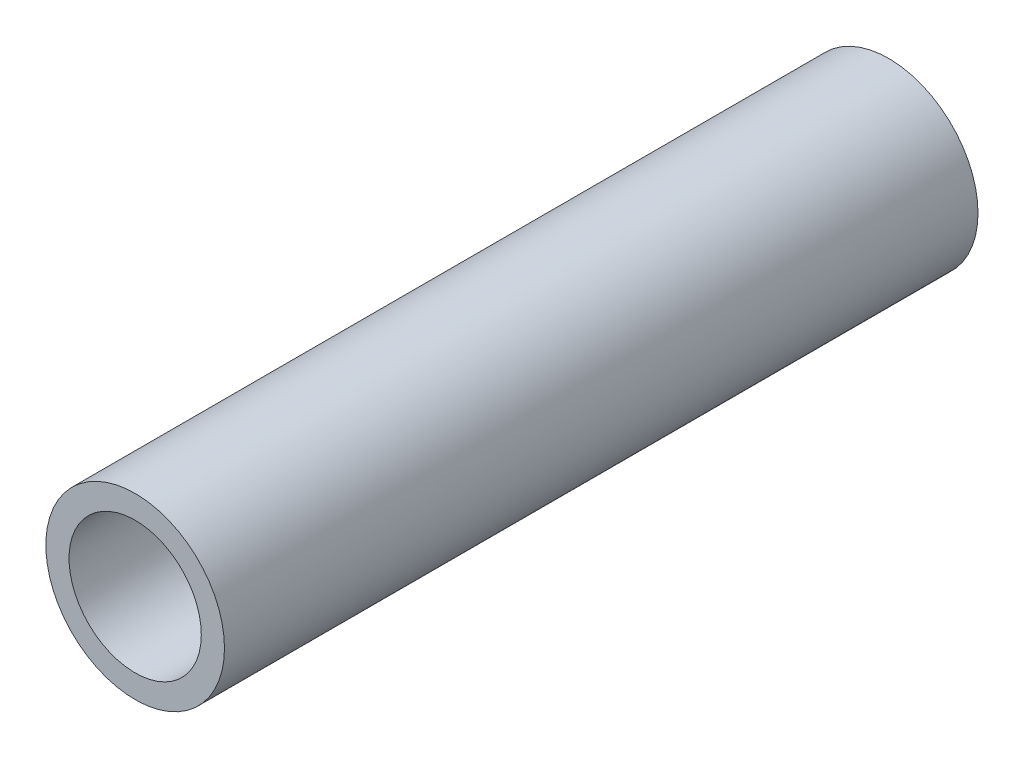
SolidWorks part; units mm, degrees
ref_plane "Front Plane" through (0, 0, 0) normal (0, 0, 1) x (1, 0, 0)
ref_plane "Top Plane" through (0, 0, 0) normal (0, 1, 0) x (1, 0, 0)
ref_plane "Right Plane" through (0, 0, 0) normal (1, 0, 0) x (0, 0, -1)
sketch "Sketch1" plane through (0, 0, 0) normal (0, 0, 1) x (1, 0, 0)
  circle A0 centre (0, 0) radius 10.668
  dimension "Pipe OD" = 21.336
extrude "Extrude-Thin1" add sketch "Sketch1" along normal mid plane 90 thin thin type one direction reverse wall 2.7686
